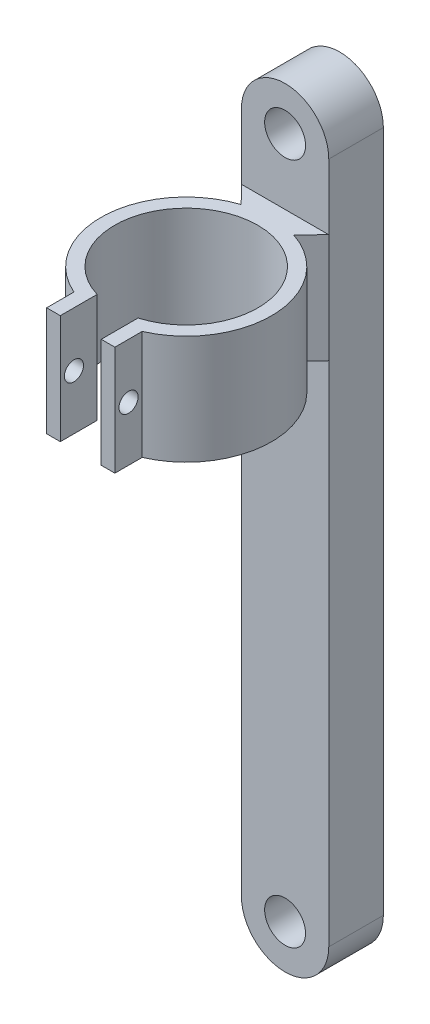
SolidWorks part; units mm, degrees
ref_plane "Front Plane" through (0, 0, 0) normal (0, 0, 1) x (1, 0, 0)
ref_plane "Top Plane" through (0, 0, 0) normal (0, 1, 0) x (1, 0, 0)
ref_plane "Right Plane" through (0, 0, 0) normal (1, 0, 0) x (0, 0, -1)
sketch "Sketch1" plane through (-856.4885, 635.7039, 371.825) normal (0, 0, 1) x (1, 0, 0)
  line L0 (0, 31.75) -> (0, -31.75) construction
  line L1 (4.064, 31.75) -> (4.064, -31.75)
  line L2 (-4.064, 31.75) -> (-4.064, -31.75)
  arc A0 (4.064, 31.75) -> (-4.064, 31.75) centre (0, 31.75) ccw
  arc A1 (-4.064, -31.75) -> (4.064, -31.75) centre (0, -31.75) ccw
  circle A2 centre (0, -31.75) radius 1.905
  circle A3 centre (0, 31.75) radius 1.905
  point P2 (0, 0)
  dimension "D3" = 3.81
  dimension "D1" = 63.5
  dimension "D2" = 8.128
extrude "Boss-Extrude1" add sketch "Sketch1" along normal blind 5.08
ref_plane "Plane1" through (0, 671.5179, 0) normal (0, 1, 0) x (1, 0, 0)
sketch "Sketch2" plane through (0, 671.5179, 0) normal (0, -1, 0) x (1, 0, 0)
  line L0 (-854.9885, 378.555) -> (-857.9885, 378.555) construction
  line L2 (-854.8883, 392.5818) -> (-854.5835, 393.8147) construction
  line L3 (-856.4885, 384.8962) -> (-856.4885, 383.4925) construction
  line L10 (-854.0518, 378.555) -> (-852.4245, 376.905)
  line L11 (-852.4245, 376.905) -> (-860.5525, 376.905)
  line L12 (-856.8086, 386.1092) -> (49143.1914, 386.1092) construction
  line L13 (-860.5525, 376.905) -> (-858.9253, 378.555)
  line L14 (-858.3935, 393.8147) -> (-858.3935, 395.924)
  line L15 (-858.3935, 395.924) -> (-859.6635, 395.924)
  line L16 (-859.6635, 395.924) -> (-859.6635, 393.384)
  line L17 (-854.5835, 393.8147) -> (-854.5835, 395.924)
  line L18 (-854.5835, 395.924) -> (-853.3135, 395.924)
  line L19 (-853.3135, 395.924) -> (-853.3135, 393.384)
  line L20 (-854.5835, 393.8147) -> (-854.5835, 392.4987)
  line L21 (-858.3935, 393.8147) -> (-858.3935, 392.4987)
  line L22 (-854.5835, 395.924) -> (-858.3935, 395.924) construction
  arc A0 (-858.3935, 392.4987) -> (-854.5835, 392.4987) centre (-856.4885, 386.1092) ccw
  arc A1 (-854.0518, 378.555) -> (-853.3135, 393.384) centre (-856.4885, 386.1092) ccw
  arc A2 (-859.6635, 393.384) -> (-858.9253, 378.555) centre (-856.4885, 386.1092) ccw
  arc A5 (-858.3935, 393.8147) -> (-854.5835, 393.8147) centre (-856.4885, 386.1092) ccw construction
  arc A7 (-858.0887, 392.5818) -> (-854.8883, 392.5818) centre (-856.4885, 386.1092) ccw construction
  point P15 (-856.4885, 376.905)
  point P16 (-856.4885, 395.924)
  dimension "D1" = 13.335
  dimension "D2" = 1.27
  dimension "D4" = 3.81
  dimension "D3" = 7.5542
  dimension "D6" = 1.27
  dimension "D7" = 2.54
extrude "Boss-Extrude2" add sketch "Sketch2" along normal blind 10.16 from offset 10.16 contours A0 L20 L17 L18 L19 A1 L10 L11 L13 A2 L16 L15 L14 L21
sketch "Sketch3" plane through (-853.3135, 0, 0) normal (1, 0, 0) x (0, 0, -1)
  line L0 (-394.654, 661.3579) -> (-394.654, 651.1979) construction
  line L1 (-395.924, 661.3579) -> (-393.384, 661.3579) construction
  line L2 (-395.924, 651.1979) -> (-393.384, 651.1979) construction
  line L4 (-395.924, 651.1979) -> (-395.924, 661.3579) construction
  line L5 (-395.924, 656.2779) -> (-393.384, 656.2779) construction
  line L6 (-393.384, 651.1979) -> (-393.384, 661.3579) construction
  circle A0 centre (-394.654, 656.2779) radius 0.889
  dimension "D1" = 1.778
extrude "Cut-Extrude1" cut sketch "Sketch3" against normal through all
equation "\"D1@Sketch1\"=\"length_side@4barlift.Assembly\""
equation "\"D1@Boss-Extrude1\"=\"thick@4barlift.Assembly\""
equation "\"D2@Sketch1\"= \"width@4barlift.Assembly\""
